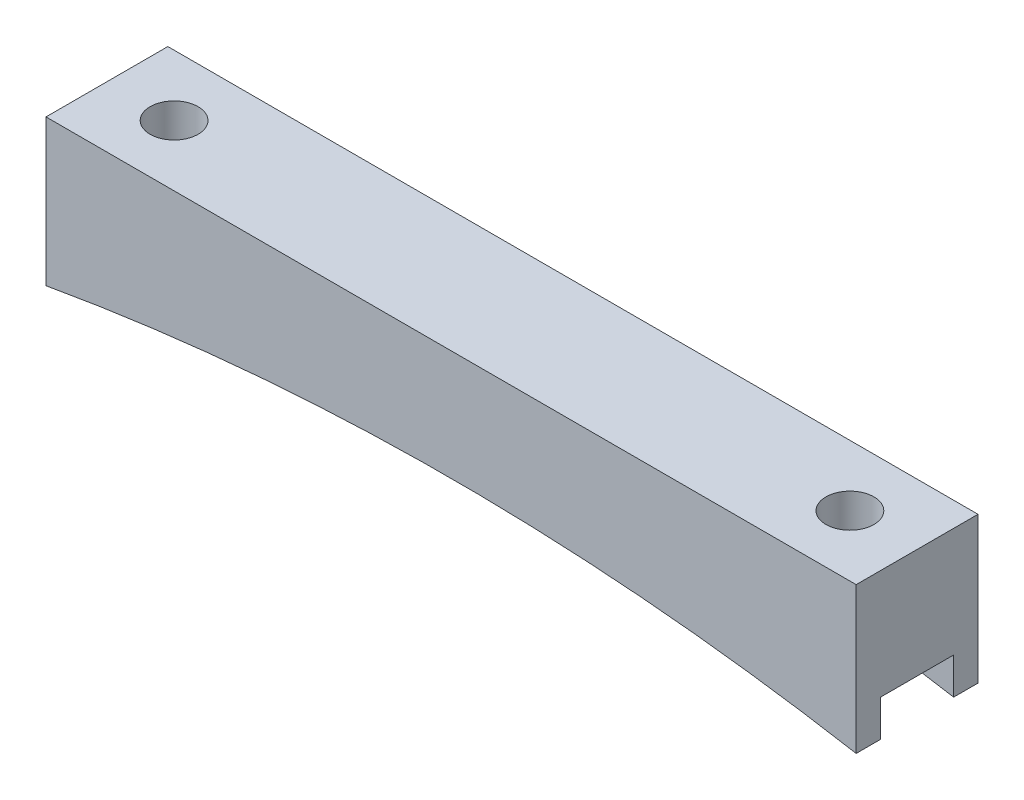
SolidWorks part; units mm, degrees
ref_plane "Front Plane" through (0, 0, 0) normal (0, 0, 1) x (1, 0, 0)
ref_plane "Top Plane" through (0, 0, 0) normal (0, 1, 0) x (1, 0, 0)
ref_plane "Right Plane" through (0, 0, 0) normal (1, 0, 0) x (0, 0, -1)
sketch "Sketch1" plane through (0, 0, 0) normal (0, 0, 1) x (1, 0, 0)
  line L0 (-42.22, 0) -> (42.22, 0)
  line L1 (-35.22, -2.54) -> (35.22, -2.54) construction
  line L2 (0, 0) -> (0, -4.6068) construction
  line L3 (42.22, 0) -> (42.22, -15.24)
  line L4 (-42.22, 0) -> (-42.22, -15.24)
  arc A0 (-42.22, -15.24) -> (42.22, -15.24) centre (0, -252.8177) cw
  point P4 (0, 0)
  point P9 (0, -2.54)
  dimension "D4" = 241.3
  dimension "D1" = 70.44
  dimension "D2" = 2.54
  dimension "D3" = 7
  dimension "D5" = 15.24
extrude "Boss-Extrude1" add sketch "Sketch1" along normal blind 12.7
sketch "Sketch2" plane through (0, 0, 0) normal (0, 1, 0) x (1, 0, 0)
  line L1 (-35.22, 0) -> (-35.22, -12.7) construction
  line L2 (-42.22, 0) -> (42.22, 0) construction
  line L3 (42.22, -12.7) -> (-42.22, -12.7) construction
  line L4 (35.22, 0) -> (35.22, -12.7) construction
  circle A0 centre (-35.22, -6.35) radius 2.5
  circle A1 centre (35.22, -6.35) radius 2.5
  circle A2 centre (-35.22, -6.35) radius 3 construction
  point P7 (-35.22, -6.35)
  dimension "D1" = 5
  dimension "D2" = 6
extrude "Cut-Extrude1" cut sketch "Sketch2" against normal through all
sketch "Sketch3" plane through (42.22, 0, 0) normal (1, 0, 0) x (0, 0, -1)
  line L0 (-12.7, -15.24) -> (0, -15.24) construction
  line L1 (-10.16, -15.24) -> (-2.54, -15.24)
  line L2 (-10.16, -15.24) -> (-10.16, -11.43)
  line L3 (-10.16, -11.43) -> (-2.54, -11.43)
  line L4 (-2.54, -15.24) -> (-2.54, -11.43)
  line L5 (-12.7, -15.24) -> (-12.7, 0) construction
  line L6 (0, -15.24) -> (0, 0) construction
  dimension "D1" = 2.54
  dimension "D2" = 2.54
  dimension "D3" = 3.81
extrude "Cut-Extrude2" cut sketch "Sketch3" against normal through all
